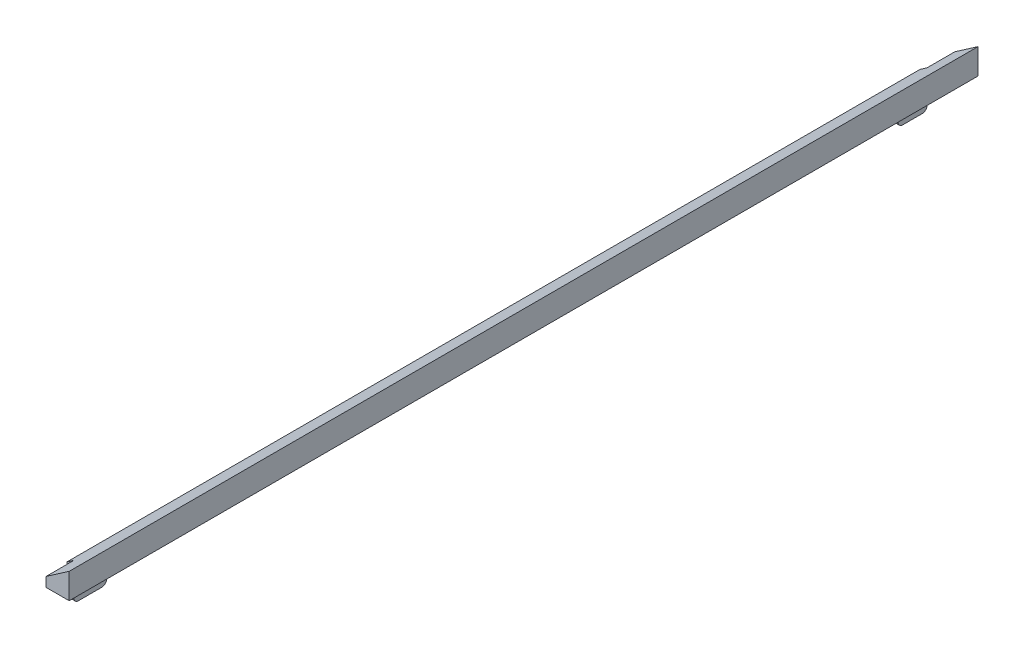
SolidWorks part; units mm, degrees
ref_plane "Front" through (0, 0, 0) normal (0, 0, 1) x (1, 0, 0)
ref_plane "Top" through (0, 0, 0) normal (0, 1, 0) x (1, 0, 0)
ref_plane "Right" through (0, 0, 0) normal (1, 0, 0) x (0, 0, -1)
sketch "Sketch1" plane through (0, 0, 0) normal (0, 0, 1) x (1, 0, 0)
  line L0 (6.5, 269) -> (6.5, -31) construction
  line L1 (0, 0) -> (6.5, 0)
  line L2 (0, 0) -> (0, 5.5)
  line L3 (0, 5.5) -> (6.5, 5.5)
  line L4 (6.5, 0) -> (6.5, 5.5)
  dimension "D1" = 5.5
extrude "Boss-Extrude1" add sketch "Sketch1" along normal offset from surface (184 mm away) 3
sketch "Sketch2" plane through (0, 0, 0) normal (0, 0, -1) x (-1, 0, 0)
  line L0 (0, 1) -> (-6.5, 5.5)
  line L1 (-6.5, 5.5) -> (0, 5.5)
  line L2 (0, 5.5) -> (0, 1)
  line L3 (0, 5.5) -> (0, 0) construction
  dimension "D1" = 1
extrude "Cut-Extrude2" cut sketch "Sketch2" against normal through all
sketch "Sketch3" plane through (0, 0, 0) normal (0, -1, 0) x (1, 0, 0)
  line L0 (0, 184) -> (0, 0) construction
  line L1 (0, 0) -> (1.5, 0)
  line L2 (0, 0) -> (0, 6.2437)
  line L3 (0, 6.2437) -> (1.5, 6.2437)
  line L4 (1.5, 0) -> (1.5, 6.2437)
  line L5 (0, 184) -> (1.5, 184)
  line L6 (0, 184) -> (0, 176.9374)
  line L7 (0, 176.9374) -> (1.5, 176.9374)
  line L8 (1.5, 184) -> (1.5, 176.9374)
  line L9 (0, 184) -> (6.5, 184) construction
extrude "Boss-Extrude2" add sketch "Sketch3" along normal offset from surface (6 mm away) 2
sketch "Sketch4" plane through (0, 0, 0) normal (-1, 0, 0) x (0, 0, 1)
  line L0 (184, -3) -> (176.9374, -3) construction
  line L2 (176.9374, -6) -> (176.9374, 0) construction
  line L3 (180.4687, -3) -> (180.4687, -6) construction
  line L5 (176.9374, -6) -> (184, -6) construction
  line L6 (176.9374, -6) -> (176.9374, 0) construction
  circle A1 centre (180.9374, -3) radius 1.4
  dimension "D1" = 2.8
  dimension "D2" = 4
extrude "Cut-Extrude3" cut sketch "Sketch4" against normal through all
ref_plane "Plane1" through (0, 0, 92) normal (0, 0, 1) x (1, 0, 0)
mirror "Mirror1" about plane through (0, 0, 92) normal (0, 0, 1) of "Cut-Extrude3"
fillet "Fillet1" radius 1 4 edges at (0.75, -6, 176.9374) (0.75, -6, 184) (0.75, -6, 0) (0.75, -6, 6.2437)
sketch "Sketch5" plane through (0, 0, 0) normal (0, 0, -1) x (-1, 0, 0)
  line L0 (-6.5, 0) -> (-6.5, 5.5)
  line L1 (-6.5, 5.5) -> (-1.5, 2.0385)
  line L2 (-6.5, 5.5) -> (0, 1) construction
  line L3 (-1.5, 2.0385) -> (-1.5, 0)
  line L4 (-1.5, 0) -> (-6.5, 0)
extrude "Boss-Extrude3" add sketch "Sketch5" along normal up to surface (6 mm away)
sketch "Sketch6" plane through (0, 0, 184) normal (0, 0, 1) x (1, 0, 0)
  line L0 (6.5, 5.5) -> (6.5, 0)
  line L1 (6.5, 0) -> (1.5, 0)
  line L2 (1.5, 0) -> (1.5, 2.0385)
  line L3 (6.5, 5.5) -> (0, 1) construction
  line L4 (1.5, 2.0385) -> (6.5, 5.5)
extrude "Boss-Extrude4" add sketch "Sketch6" along normal up to surface (6 mm away)
